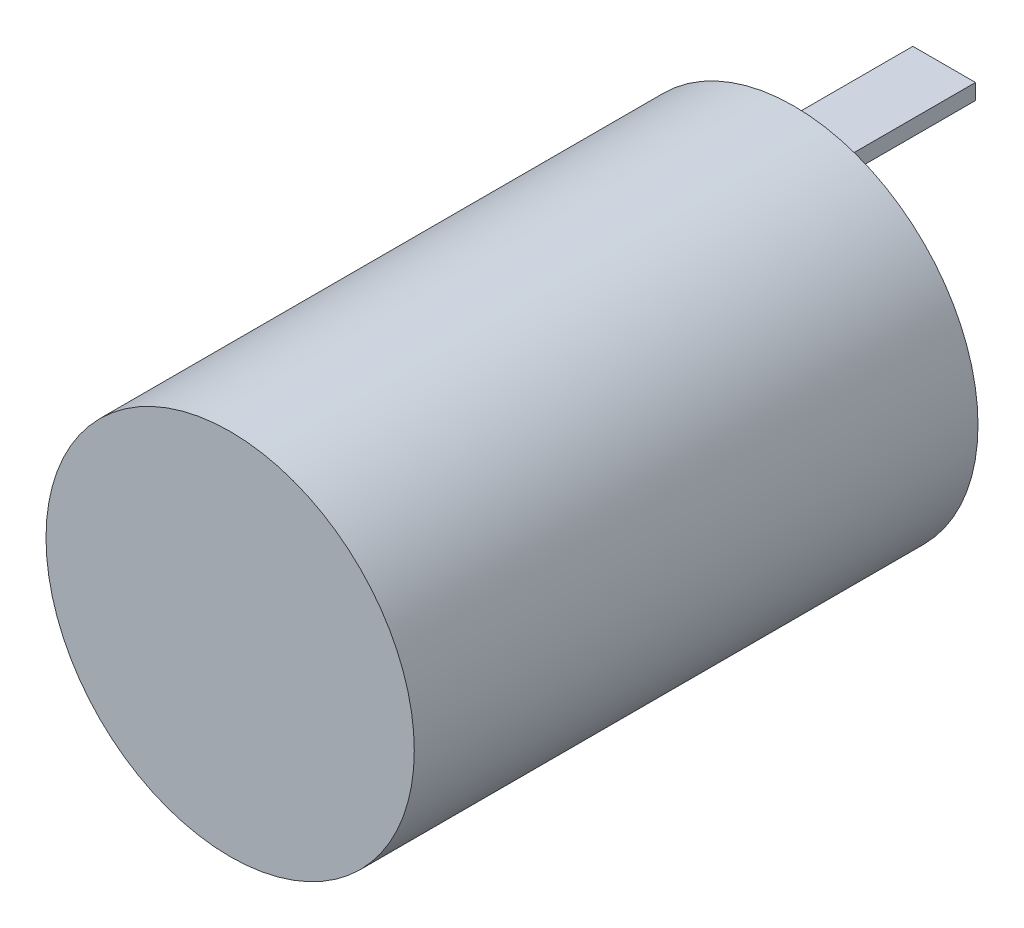
SolidWorks part; units mm, degrees
ref_plane "Front Plane" through (0, 0, 0) normal (0, 0, 1) x (1, 0, 0)
ref_plane "Top Plane" through (0, 0, 0) normal (0, 1, 0) x (1, 0, 0)
ref_plane "Right Plane" through (0, 0, 0) normal (1, 0, 0) x (0, 0, -1)
sketch "Sketch1" plane through (0, 0, 0) normal (0, 0, 1) x (1, 0, 0)
  circle A0 centre (0, 0) radius 18.669
  dimension "D1" = 37.338
extrude "Boss-Extrude1" add sketch "Sketch1" along normal blind 57.15
sketch "Sketch2" plane through (0, 0, 0) normal (0, 0, -1) x (-1, 0, 0)
  line L1 (-3.175, 14.7003) -> (3.175, 14.7003)
  line L2 (-3.175, 14.7003) -> (-3.175, 13.1128)
  line L3 (-3.175, 13.1128) -> (3.175, 13.1128)
  line L4 (3.175, 14.7003) -> (3.175, 13.1128)
  line L5 (-3.175, 14.7003) -> (3.175, 13.1128) construction
  line L6 (-3.175, 13.1128) -> (3.175, 14.7003) construction
  line L7 (-3.175, -13.1128) -> (3.175, -13.1128)
  line L8 (-3.175, -13.1128) -> (-3.175, -14.7003)
  line L9 (-3.175, -14.7003) -> (3.175, -14.7003)
  line L10 (3.175, -13.1128) -> (3.175, -14.7003)
  line L11 (-3.175, -13.1128) -> (3.175, -14.7003) construction
  line L12 (-3.175, -14.7003) -> (3.175, -13.1128) construction
  circle A0 centre (0, 0) radius 13.9065 construction
  circle A1 centre (0, 0) radius 18.669
  circle A2 centre (0, 0) radius 18.669
  point P1 (0, 13.9065)
  point P9 (0, -13.9065)
  dimension "D2" = 4.7625
  dimension "D3" = 6.35
  dimension "D4" = 1.5875
  dimension "D1" = 0
extrude "Boss-Extrude2" add sketch "Sketch2" along normal blind 15.24 contours L4 L1 L2 L3 | L10 L7 L8 L9
